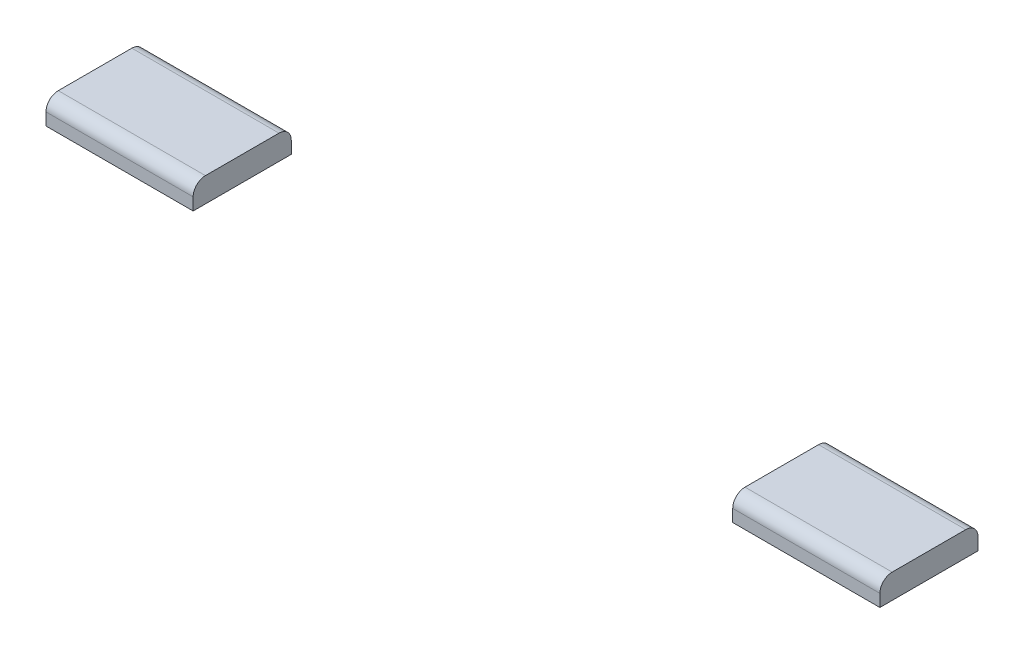
SolidWorks part; units mm, degrees
material "Rubber"
ref_plane "Front Plane" through (0, 0, 0) normal (0, 0, 1) x (1, 0, 0)
ref_plane "Top Plane" through (0, 0, 0) normal (0, 1, 0) x (1, 0, 0)
ref_plane "Right Plane" through (0, 0, 0) normal (1, 0, 0) x (0, 0, -1)
sketch "Sketch1" plane through (0, 0, 0) normal (0, 1, 0) x (1, 0, 0)
  line L1 (0, 0) -> (215.9, 0)
  line L2 (0, 0) -> (0, 25.4)
  line L3 (0, 25.4) -> (215.9, 25.4)
  line L4 (215.9, 0) -> (215.9, 25.4)
  dimension "D1" = 215.9
  dimension "D2" = 25.4
extrude "Boss-Extrude1" add sketch "Sketch1" along normal blind 6.35
fillet "Fillet1" radius 3.175 2 edges at (107.95, 6.35, -25.4) (107.95, 6.35, 0)
sketch "Sketch2" plane through (0, 0, 0) normal (0, -1, 0) x (1, 0, 0)
  line L0 (0, 0) -> (215.9, 0) construction
  line L1 (38.1, 0) -> (177.8, 0)
  line L2 (38.1, 0) -> (38.1, -25.4)
  line L3 (38.1, -25.4) -> (177.8, -25.4)
  line L4 (177.8, 0) -> (177.8, -25.4)
  line L5 (215.9, -25.4) -> (0, -25.4) construction
  line L6 (0, -25.4) -> (0, 0) construction
  line L7 (215.9, 0) -> (215.9, -25.4) construction
  dimension "D1" = 38.1
  dimension "D2" = 38.1
extrude "Cut-Extrude1" cut sketch "Sketch2" against normal through all
